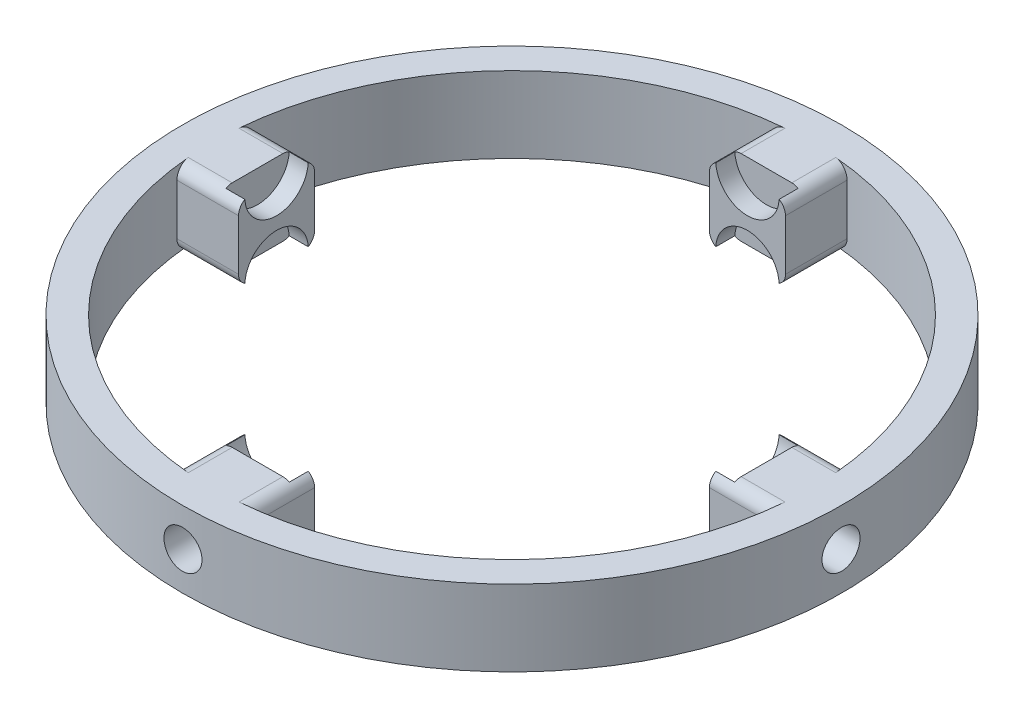
SolidWorks part; units mm, degrees
material "ABS"
ref_plane "Front Plane" through (0, 0, 0) normal (0, 0, 1) x (1, 0, 0)
ref_plane "Top Plane" through (0, 0, 0) normal (0, 1, 0) x (1, 0, 0)
ref_plane "Right Plane" through (0, 0, 0) normal (1, 0, 0) x (0, 0, -1)
sketch "Sketch1" plane through (0, 0, 0) normal (0, 1, 0) x (1, 0, 0)
  circle A0 centre (0, 0) radius 23.625
  circle A1 centre (0, 0) radius 26
  dimension "D1" = 47.25
  dimension "D2" = 52
extrude "Boss-Extrude1" add sketch "Sketch1" along normal blind 6
sketch "Sketch2" plane through (0, 6, 0) normal (0, 1, 0) x (1, 0, 0)
  line L0 (-25.8263, 0) -> (0, 0) construction
  line L1 (-25.8263, -3) -> (-18.5763, -3)
  line L2 (-25.8263, -3) -> (-25.8263, 3)
  line L3 (-25.8263, 3) -> (-18.5763, 3)
  line L4 (-18.5763, -3) -> (-18.5763, 3)
  line L5 (-25.8263, -3) -> (-18.5763, 3) construction
  line L6 (-25.8263, 3) -> (-18.5763, -3) construction
  circle A0 centre (0, 0) radius 26 construction
  point P6 (0, 0)
  dimension "D1" = 7.25
  dimension "D2" = 6
extrude "Boss-Extrude2" add sketch "Sketch2" against normal up to surface (6 mm away) up to face at (0, 0, 26)
pattern_circular "CirPattern1" count 4 over 360 about axis through (0, 0, 0) along (0, 1, 0) of "Boss-Extrude2"
sketch "Sketch3" plane through (-18.5763, 0, 0) normal (1, 0, 0) x (0, 0, -1)
  line L0 (3, 0) -> (-3, 0) construction
  line L1 (-3, 6) -> (3, 6) construction
  circle A0 centre (0, 6) radius 2.5
  circle A1 centre (0, 0) radius 2.5
  dimension "D1" = 5
  dimension "D3" = 5
  dimension "D2" = 6
  dimension "D4" = 6
extrude "Cut-Extrude1" cut sketch "Sketch3" against normal blind 1.5
pattern_circular "CirPattern2" count 4 over 360 about axis through (0, 0, 0) along (0, 1, 0) of "Cut-Extrude1"
fillet "Fillet1" radius 1 48 edges at (-18.5763, 0, 2.75) (-18.5763, 6, -2.75) (-19.3263, 6, 2.5) (-19.3263, 6, -2.5) (-19.3263, 0, 2.5) (-19.3263, 0, -2.5) (-2.75, 0, -18.5763) (2.75, 6, -18.5763) (18.5763, 0, -2.75) (18.5763, 6, 2.75) (2.75, 0, 18.5763) (-2.75, 6, 18.5763) (-2.5, 6, -19.3263) (2.5, 6, -19.3263) (19.3263, 0, -2.5) (19.3263, 0, 2.5) (19.3263, 6, -2.5) (19.3263, 6, 2.5) (2.5, 0, 19.3263) (-2.5, 0, 19.3263) (-21.005, 6, 3) (-2.5, 0, -19.3263) (2.5, 0, -19.3263) (-18.5763, 6, 2.75) (2.5, 6, 19.3263) (-2.5, 6, 19.3263) (-21.005, 6, -3) (-21.005, 0, -3) (-18.5763, 0, -2.75) (-21.005, 0, 3) (3, 6, 21.005) (2.75, 6, 18.5763) (-3, 6, 21.005) (-3, 0, 21.005) (-2.75, 0, 18.5763) (3, 0, 21.005) (21.005, 6, -3) (18.5763, 6, -2.75) (21.005, 6, 3) (21.005, 0, 3) (18.5763, 0, 2.75) (21.005, 0, -3) (-3, 6, -21.005) (-2.75, 6, -18.5763) (3, 6, -21.005) (3, 0, -21.005) (2.75, 0, -18.5763) (-3, 0, -21.005)
ref_plane "Plane1" through (0, 0, 26) normal (0, 0, 1) x (1, 0, 0)
sketch "Sketch4" plane through (0, 0, 26) normal (0, 0, 1) x (1, 0, 0)
  circle A0 centre (0, 3) radius 1.5
  point P2 (0, 0)
  dimension "D1" = 3
  dimension "D2" = 3
extrude "Cut-Extrude2" cut sketch "Sketch4" against normal blind 4
pattern_circular "CirPattern4" count 4 over 360 about axis through (0, 0, 0) along (0, 1, 0) of "Cut-Extrude2"
